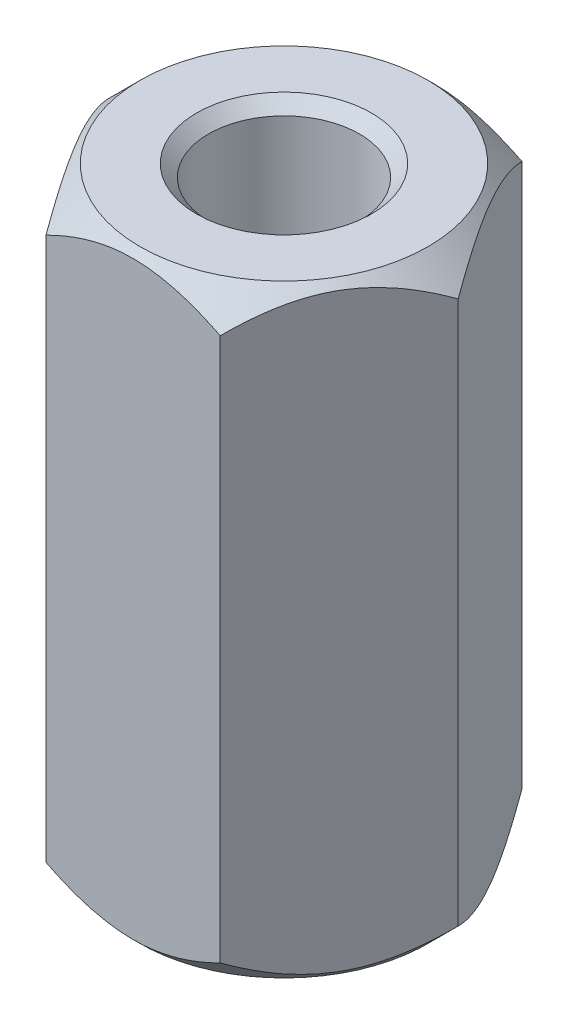
SolidWorks part; units mm, degrees
ref_plane "Front Plane" through (0, 0, 0) normal (0, 0, 1) x (1, 0, 0)
ref_plane "Top Plane" through (0, 0, 0) normal (0, 1, 0) x (1, 0, 0)
ref_plane "Right Plane" through (0, 0, 0) normal (1, 0, 0) x (0, 0, -1)
sketch "Sketch1" plane through (0, 0, 0) normal (0, 1, 0) x (1, 0, 0)
  line L1 (1.4434, 2.5) -> (-1.4434, 2.5)
  line L2 (-1.4434, 2.5) -> (-2.8868, 0)
  line L3 (-2.8868, 0) -> (-1.4434, -2.5)
  line L4 (-1.4434, -2.5) -> (1.4434, -2.5)
  line L5 (1.4434, -2.5) -> (2.8868, 0)
  line L6 (2.8868, 0) -> (1.4434, 2.5)
  circle A0 centre (0, 0) radius 2.5 construction
  circle A1 centre (0, 0) radius 1.25
  dimension "D1" = 5
  dimension "D2" = 2.5
extrude "Boss-Extrude1" add sketch "Sketch1" along normal blind 10
chamfer "Chamfer1" distance 0.2 angle 45 2 edges at (0, 0, 1.25) (0, 10, 1.25)
sketch "Sketch2" plane through (0, 0, 0) normal (0, 0, 1) x (1, 0, 0)
  line L0 (2.3868, 10) -> (2.8868, 9.5)
  line L1 (1.4434, 10) -> (2.8868, 10) construction
  line L2 (2.8868, 10) -> (2.8868, 0) construction
  line L3 (2.8868, 9.5) -> (2.8868, 10)
  line L4 (2.8868, 10) -> (2.3868, 10)
  line L5 (2.3868, 0) -> (2.8868, 0)
  line L6 (1.4434, 0) -> (2.8868, 0) construction
  line L7 (2.8868, 0) -> (2.8868, 0.5)
  line L8 (2.8868, 0.5) -> (2.3868, 0)
  line L9 (0, 0) -> (0, 6.2275) construction
  dimension "D1" = 0.5
revolve "Cut-Revolve1" cut sketch "Sketch2" angle 360 about L9
